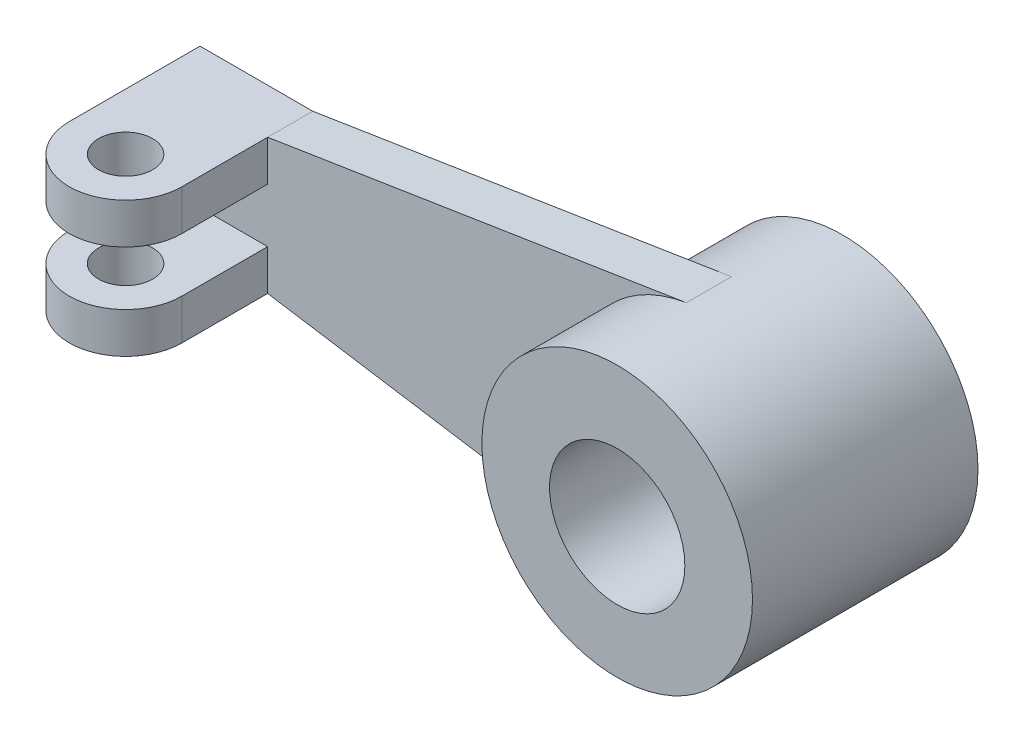
SolidWorks part; units mm, degrees
ref_plane "Front Plane" through (0, 0, 0) normal (0, 0, 1) x (1, 0, 0)
ref_plane "Top Plane" through (0, 0, 0) normal (0, 1, 0) x (1, 0, 0)
ref_plane "Right Plane" through (0, 0, 0) normal (1, 0, 0) x (0, 0, -1)
sketch "Sketch1" plane through (0, 0, 0) normal (0, 0, 1) x (1, 0, 0)
  circle A0 centre (0, 0) radius 30
  circle A1 centre (0, -1.0072) radius 15
  dimension "D1" = 30
  dimension "D2" = 60
extrude "Boss-Extrude1" add sketch "Sketch1" along normal mid plane 50
sketch "Sketch2" plane through (0, 0, 0) normal (0, 0, 1) x (1, 0, 0)
  line L0 (0, 0) -> (-79.7495, 0) construction
  line L1 (-122.5, -15) -> (-122.5, 15)
  line L2 (-122.5, 15) -> (-97.5, 15)
  line L3 (-122.5, -15) -> (-97.5, -15)
  line L4 (-97.5, 15) -> (-4.6717, 29.634)
  line L5 (-97.5, -15) -> (-4.6717, -29.634)
  circle A0 centre (0, 0) radius 30 construction
  circle A1 centre (0, 0) radius 30
  point P7 (-122.5, 0)
  dimension "D1" = 30
  dimension "D2" = 25
  dimension "D3" = 25
  dimension "D4" = 122.5
extrude "Boss-Extrude3" add sketch "Sketch2" along normal mid plane 10
sketch "Sketch4" plane through (0, -15, 0) normal (0, -1, 0) x (-1, 0, 0)
  line L0 (122.5, -5) -> (122.5, -24)
  line L1 (122.5, -5) -> (97.5, -5) construction
  line L2 (97.5, -5) -> (97.5, -24)
  line L3 (122.5, -24) -> (97.5, -24)
  circle A0 centre (110, -24) radius 6
  arc A1 (97.5, -24) -> (122.5, -24) centre (110, -24) ccw
  line M4 (97.5, -5) -> (122.5, -5)
  dimension "D1" = 12
  dimension "D2" = 25
  dimension "D3" = 19
  dimension "D4" = 110
extrude "Boss-Extrude4" add sketch "Sketch4" against normal blind 9 contours L3 A1 A0 | A0 L3 L0 L2 M4
mirror "Mirror1" about plane through (0, 0, 0) normal (0, 1, 0) of "Boss-Extrude4"
